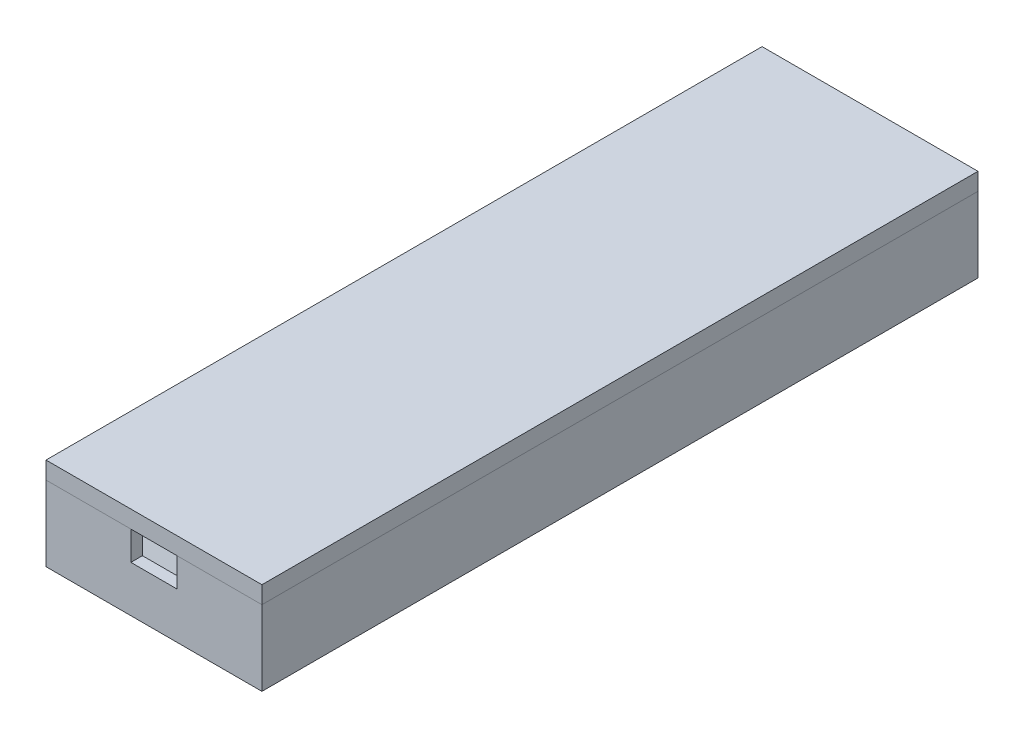
SolidWorks part; units mm, degrees
ref_plane "Front Plane" through (0, 0, 0) normal (0, 0, 1) x (1, 0, 0)
ref_plane "Top Plane" through (0, 0, 0) normal (0, 1, 0) x (1, 0, 0)
ref_plane "Right Plane" through (0, 0, 0) normal (1, 0, 0) x (0, 0, -1)
sketch "Sketch1" plane through (0, 0, 0) normal (0, 0, 1) x (1, 0, 0)
  line L0 (-18.6969, 0) -> (18.6969, 0)
  line L1 (18.6969, 0) -> (18.6969, 13)
  line L2 (18.6969, 13) -> (15.6969, 13)
  line L3 (15.6969, 13) -> (0, 3)
  line L4 (0, 3) -> (-15.6969, 13)
  line L5 (-15.6969, 13) -> (-18.6969, 13)
  line L6 (-18.6969, 13) -> (-18.6969, 0)
  line L7 (0, 3) -> (0, 0) construction
  line L8 (0, 3) -> (0, 16.1511) construction
  line L9 (0, 3) -> (-2.4751, 1.4232) construction
  dimension "D1" = 115
  dimension "D2" = 10
  dimension "D3" = 13
  dimension "D4" = 3
extrude "Boss-Extrude1" add sketch "Sketch1" along normal blind 120
sketch "Sketch2" plane through (0, 0, 0) normal (0, 0, -1) x (-1, 0, 0)
  line L1 (-18.6969, 0) -> (18.6969, 0)
  line L2 (-18.6969, 0) -> (-18.6969, 13)
  line L3 (-18.6969, 13) -> (18.6969, 13)
  line L4 (18.6969, 0) -> (18.6969, 13)
extrude "Boss-Extrude2" add sketch "Sketch2" along normal blind 2
sketch "Sketch3" plane through (0, 0, 120) normal (0, 0, 1) x (1, 0, 0)
  line L1 (-18.6969, 0) -> (18.6969, 0)
  line L2 (-18.6969, 0) -> (-18.6969, 13)
  line L3 (-18.6969, 13) -> (18.6969, 13)
  line L4 (18.6969, 0) -> (18.6969, 13)
extrude "Boss-Extrude3" add sketch "Sketch3" along normal blind 2
sketch "Sketch5" plane through (0, 13, 0) normal (0, 1, 0) x (1, 0, 0)
  line L1 (-18.6969, 2) -> (18.6969, 2)
  line L2 (-18.6969, 2) -> (-18.6969, -122)
  line L3 (-18.6969, -122) -> (18.6969, -122)
  line L4 (18.6969, 2) -> (18.6969, -122)
extrude "Boss-Extrude4" add sketch "Sketch5" along normal blind 3 separate body
sketch "Sketch6" plane through (0, 0, 122) normal (0, 0, 1) x (1, 0, 0)
  line L0 (0, 0) -> (0, 32.3003) construction
  line L1 (-18.6969, 0) -> (18.6969, 0) construction
  line L2 (0, 32.3003) -> (0.4733, 32.3003) construction
  line L3 (18.6969, 13) -> (-18.6969, 13) construction
  line L4 (-4, 13) -> (4, 13)
  line L5 (-4, 13) -> (-4, 8)
  line L6 (-4, 8) -> (4, 8)
  line L7 (4, 13) -> (4, 8)
  dimension "D1" = 5
  dimension "D2" = 8
extrude "Cut-Extrude1" cut sketch "Sketch6" against normal blind 3
